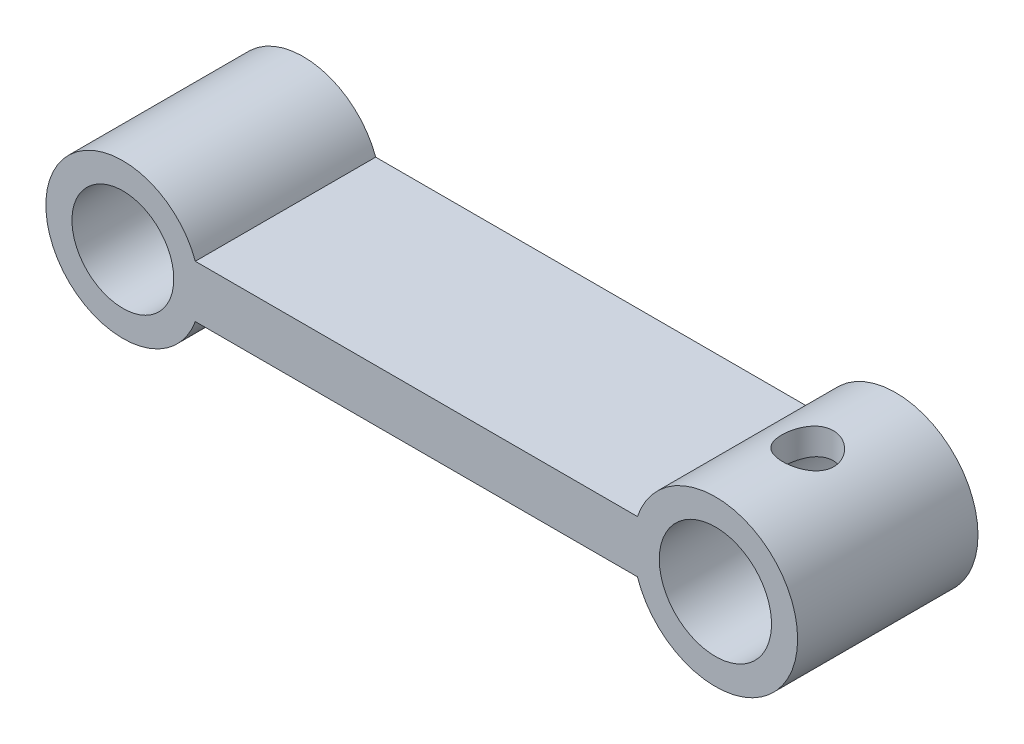
SolidWorks part; units mm, degrees
material "ABS"
ref_plane "Front Plane" through (0, 0, 0) normal (0, 0, 1) x (1, 0, 0)
ref_plane "Top Plane" through (0, 0, 0) normal (0, 1, 0) x (1, 0, 0)
ref_plane "Right Plane" through (0, 0, 0) normal (1, 0, 0) x (0, 0, -1)
sketch "Sketch1" plane through (0, 0, 0) normal (0, 0, 1) x (1, 0, 0)
  line L0 (-11.2441, 0) -> (11.4559, 0) construction
  line L1 (0, 1) -> (0, -1) construction
  line L2 (8.4688, 1) -> (-8.4688, 1)
  line L4 (8.4688, -1) -> (-8.4688, -1)
  circle A0 centre (-11.2441, 0) radius 1.95
  arc A1 (-8.4688, 1) -> (-8.4688, -1) centre (-11.2441, 0) ccw
  arc A2 (8.4688, -1) -> (8.4688, 1) centre (11.4559, 0) ccw
  circle A3 centre (11.4559, 0) radius 2.15
  point P10 (0, 0)
  dimension "D1" = 22.7
  dimension "D2" = 3.9
  dimension "D3" = 1
  dimension "D6" = 2
  dimension "D7" = 4.3
  dimension "D8" = 1
  dimension "D4" = 1
  dimension "D5" = 1
extrude "main body" add sketch "Sketch1" along normal blind 6.91
sketch "Sketch2" plane through (0, 1, 0) normal (0, 1, 0) x (1, 0, 0)
  line L0 (11.5373, 0) -> (11.5373, -6.91) construction
  line L3 (14.6059, 0) -> (8.4688, 0) construction
  line L6 (8.4688, -6.91) -> (14.6059, -6.91) construction
  circle A0 centre (11.5373, -3.455) radius 1
  dimension "D1" = 2
extrude "tendon hole" cut sketch "Sketch2" against normal mid plane 15
